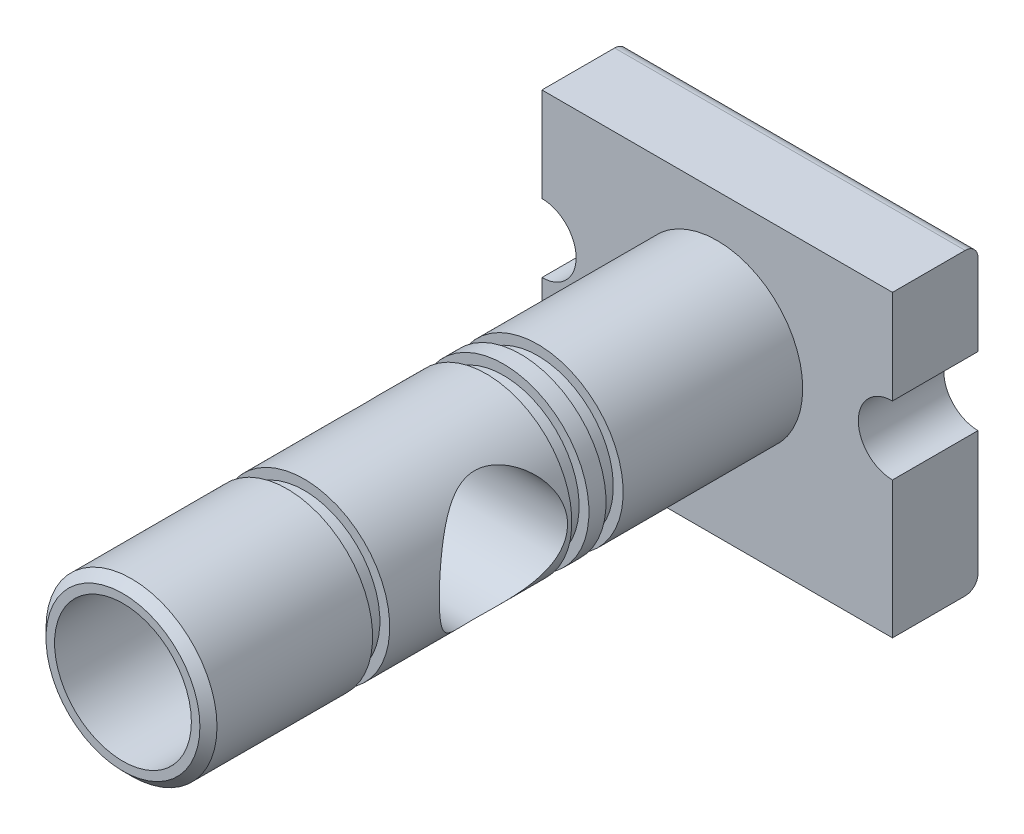
SolidWorks part; units mm, degrees
ref_plane "Front Plane" through (0, 0, 0) normal (0, 0, 1) x (1, 0, 0)
ref_plane "Top Plane" through (0, 0, 0) normal (0, 1, 0) x (1, 0, 0)
ref_plane "Right Plane" through (0, 0, 0) normal (1, 0, 0) x (0, 0, -1)
sketch "Sketch1" plane through (0, 0, 0) normal (0, 0, 1) x (1, 0, 0)
  line L0 (-41, -8) -> (-41, -40)
  line L1 (-41, 30) -> (41, 30)
  line L2 (-41, 30) -> (-41, 8)
  line L3 (-41, -40) -> (41, -40)
  line L4 (41, 30) -> (41, 8)
  line L5 (41, -8) -> (41, -40)
  arc A0 (-41, -8) -> (-41, 8) centre (-41, 0) ccw
  arc A1 (41, 8) -> (41, -8) centre (41, 0) ccw
  dimension "D5" = 16
  dimension "D1" = 70
  dimension "D2" = 82
  dimension "D3" = 41
  dimension "D4" = 40
extrude "Boss-Extrude1" add sketch "Sketch1" along normal blind 20
sketch "Sketch2" plane through (0, 0, 20) normal (0, 0, 1) x (1, 0, 0)
  circle A0 centre (0, 0) radius 20
  dimension "D1" = 40
extrude "Boss-Extrude2" add sketch "Sketch2" along normal blind 139
sketch "Sketch3" plane through (0, 0, 0) normal (1, 0, 0) x (0, 0, -1)
  line L0 (-20, 8) -> (-20, 30) construction
  circle A0 centre (-90, 0) radius 15
  point P4 (0, 0)
  dimension "D1" = 30
  dimension "D2" = 70
extrude "Cut-Extrude1" cut sketch "Sketch3" against normal through all both and the other way through all
sketch "Sketch4" plane through (0, 0, 0) normal (1, 0, 0) x (0, 0, -1)
  line L0 (-20, 20) -> (-159, 20) construction
  line L1 (-66, 20) -> (-62, 20)
  line L2 (-66, 20) -> (-66, 17.7)
  line L3 (-66, 17.7) -> (-62, 17.7)
  line L4 (-62, 20) -> (-62, 17.7)
  line L5 (-20, 8) -> (-20, 30) construction
  line L6 (-74, 20) -> (-70, 20)
  line L7 (-74, 20) -> (-74, 17.7)
  line L8 (-74, 17.7) -> (-70, 17.7)
  line L9 (-70, 20) -> (-70, 17.7)
  line L10 (-120.6, 20) -> (-116.6, 20)
  line L11 (-120.6, 20) -> (-120.6, 17.7)
  line L12 (-120.6, 17.7) -> (-116.6, 17.7)
  line L13 (-116.6, 20) -> (-116.6, 17.7)
  line L14 (0, 0) -> (-203.4126, 0) construction
  dimension "D1" = 2.3
  dimension "D2" = 4
  dimension "D3" = 4
  dimension "D4" = 4
  dimension "D5" = 4
  dimension "D6" = 42
  dimension "D7" = 42.6
revolve "Cut-Revolve1" cut sketch "Sketch4" angle 360 about L14
sketch "Sketch5" plane through (0, 0, 159) normal (0, 0, 1) x (1, 0, 0)
  circle A0 centre (0, 0) radius 16
  dimension "D1" = 32
extrude "Cut-Extrude2" cut sketch "Sketch5" against normal blind 35.4
sketch "Sketch6" plane through (0, 0, 123.6) normal (0, 0, 1) x (1, 0, 0)
  circle A0 centre (0, 0) radius 9.5
  dimension "D1" = 19
extrude "Cut-Extrude3" cut sketch "Sketch6" against normal blind 22
chamfer "Chamfer1" distance 2 1 edges at (20, 0, 159)
fillet "Fillet1" radius 3 2 edges at (0, -40, 0) (0, 30, 0)
